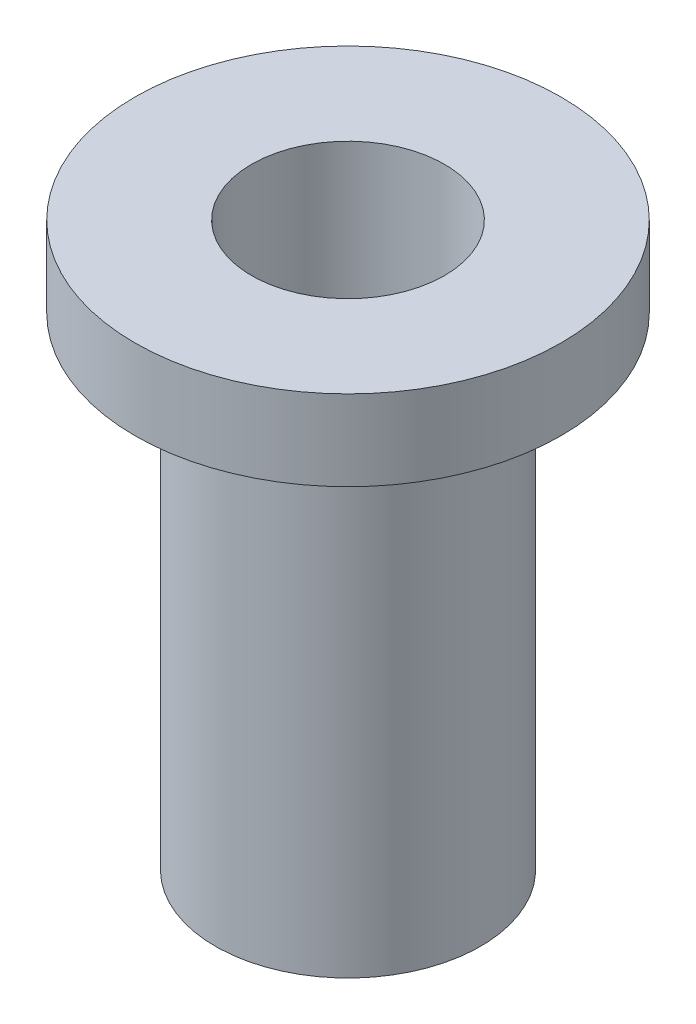
SolidWorks part; units mm, degrees
ref_plane "Front Plane" through (0, 0, 0) normal (0, 0, 1) x (1, 0, 0)
ref_plane "Top Plane" through (0, 0, 0) normal (0, 1, 0) x (1, 0, 0)
ref_plane "Right Plane" through (0, 0, 0) normal (1, 0, 0) x (0, 0, -1)
sketch "Sketch2" plane through (0, 0, 0) normal (0, 0, 1) x (1, 0, 0)
  line L0 (-1.65, 0) -> (-1.65, -6)
  line L1 (55, 0) -> (-55, 0) construction
  line L2 (-1.65, -6) -> (0, -6)
  line L3 (0, -55) -> (0, 55) construction
  line L4 (-1.65, 0) -> (-2.65, 0)
  line L5 (-2.65, 0) -> (-2.65, 1)
  line L6 (0, 2) -> (0, -49998) construction
  line L7 (0, 1) -> (0, -6)
  line L8 (-2.65, 1) -> (0, 1)
  dimension "D4" = 1
  dimension "D1" = 1.65
  dimension "D2" = 6
  dimension "D3" = 1
revolve "Revolve2" add sketch "Sketch2" angle 360 about L6
sketch "Sketch3" plane through (0, 1, 0) normal (0, 1, 0) x (1, 0, 0)
  circle A0 centre (0, 0) radius 1.2
extrude "Cut-Extrude1" cut sketch "Sketch3" against normal offset from surface (5.8 mm away) 1.2 up to face at (-1.65, -6, 0)
